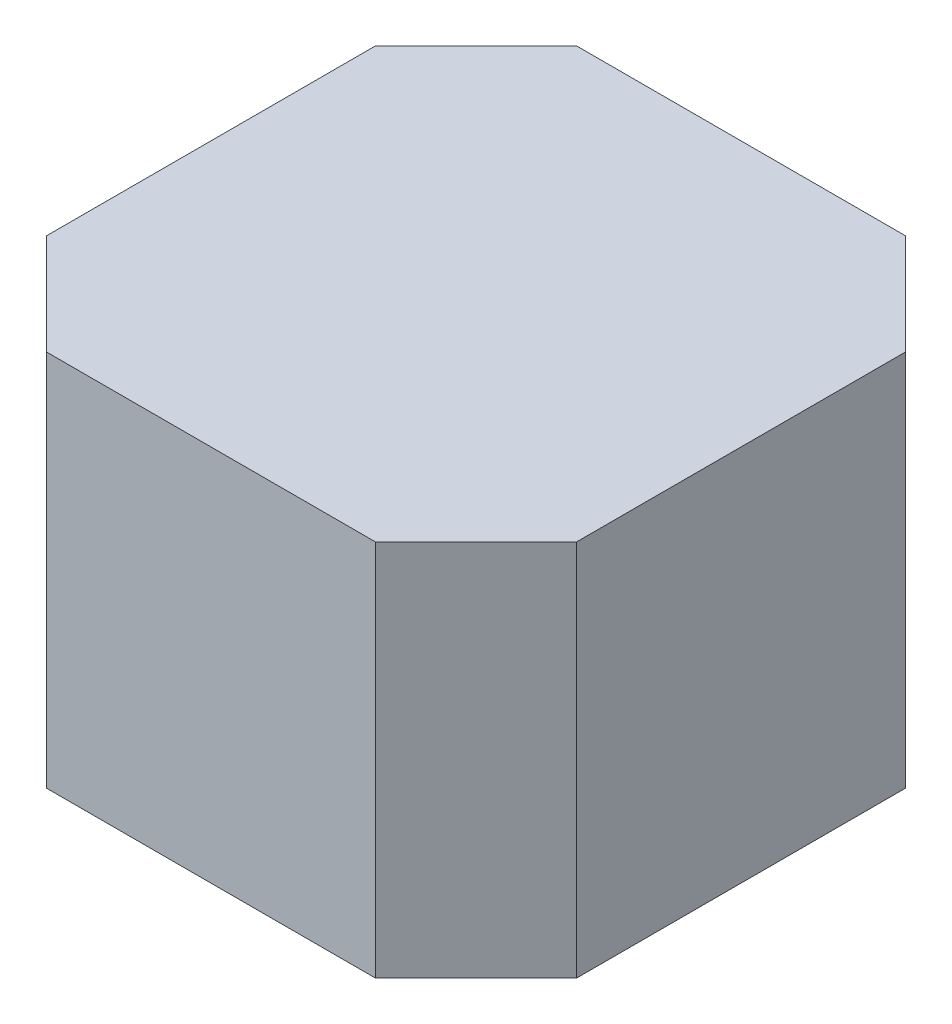
SolidWorks part; units mm, degrees
ref_plane "Front" through (0, 0, 0) normal (0, 0, 1) x (1, 0, 0)
ref_plane "Top" through (0, 0, 0) normal (0, 1, 0) x (1, 0, 0)
ref_plane "Right" through (0, 0, 0) normal (1, 0, 0) x (0, 0, -1)
sketch "Sketch1" plane through (0, 0, 0) normal (0, 1, 0) x (1, 0, 0)
  line L1 (-21.05, -21.05) -> (21.05, -21.05)
  line L2 (-21.05, -21.05) -> (-21.05, 21.05)
  line L3 (-21.05, 21.05) -> (21.05, 21.05)
  line L4 (21.05, -21.05) -> (21.05, 21.05)
  line L5 (-21.05, -21.05) -> (21.05, 21.05) construction
  line L6 (-21.05, 21.05) -> (21.05, -21.05) construction
  point P0 (0, 0)
  dimension "D1" = 42.1
extrude "Boss-Extrude1" add sketch "Sketch1" along normal blind 30
chamfer "Chamfer2" distance 8 angle 45 4 edges at (-21.05, 15, -21.05) (21.05, 15, -21.05) (21.05, 15, 21.05) (-21.05, 15, 21.05)
